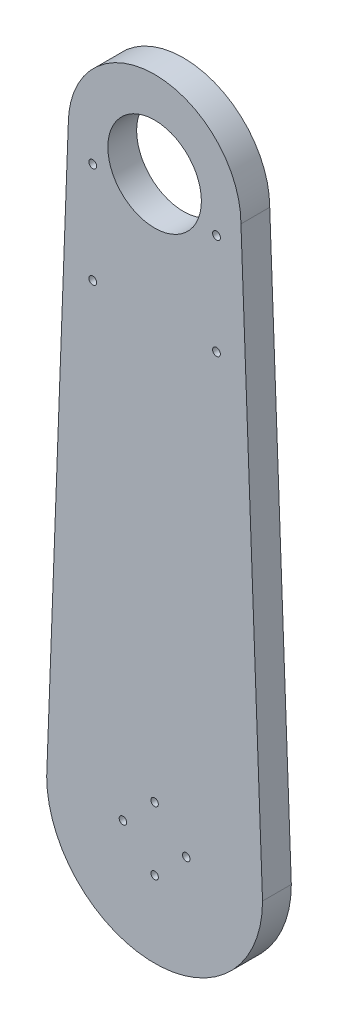
SolidWorks part; units mm, degrees
ref_plane "Front Plane" through (0, 0, 0) normal (0, 0, 1) x (1, 0, 0)
ref_plane "Top Plane" through (0, 0, 0) normal (0, 1, 0) x (1, 0, 0)
ref_plane "Right Plane" through (0, 0, 0) normal (1, 0, 0) x (0, 0, -1)
sketch "Sketch1" plane through (0, 0, 0) normal (0, 0, 1) x (1, 0, 0)
  line L0 (-30, 200) -> (-37.5, 0)
  line L1 (30, 200) -> (37.5, 0)
  circle A0 centre (0, 0) radius 37.5
  circle A1 centre (0, 200) radius 30
  dimension "D1" = 75
  dimension "D2" = 60
  dimension "D3" = 200
extrude "Boss-Extrude1" add sketch "Sketch1" along normal blind 10 contours A1 L0 A0 L1 | A1 | A0 L0
sketch "Sketch3" plane through (0, 0, 0) normal (0, 0, -1) x (-1, 0, 0)
  circle A0 centre (0, 200) radius 16.25
  dimension "D1" = 32.5
extrude "Cut-Extrude4" cut sketch "Sketch3" against normal up to next
sketch "Sketch4" plane through (0, 0, 0) normal (0, 0, -1) x (-1, 0, 0)
  circle A0 centre (0, 0) radius 11 construction
  circle A1 centre (0, 11) radius 1.3
  circle A3 centre (11, 0) radius 1.3
  circle A4 centre (0, -11) radius 1.3
  circle A5 centre (-11, 0) radius 1.3
  point P16 (0, 0)
  dimension "D1" = 2.6
  dimension "D2" = 22
  dimension "D3" = 4
extrude "Cut-Extrude5" cut sketch "Sketch4" against normal up to next
sketch "Sketch5" plane through (0, 0, 0) normal (0, 0, -1) x (-1, 0, 0)
  line L1 (-14.5, 211.25) -> (14.5, 211.25) construction
  line L2 (-14.5, 211.25) -> (-14.5, 164.25) construction
  line L3 (-14.5, 164.25) -> (14.5, 164.25) construction
  line L4 (14.5, 211.25) -> (14.5, 164.25) construction
  line L5 (-14.5, 211.25) -> (14.5, 164.25) construction
  line L6 (-14.5, 164.25) -> (14.5, 211.25) construction
  line L10 (-21.5, 192.25) -> (21.5, 192.25) construction
  line L11 (-21.5, 192.25) -> (-21.5, 157.25) construction
  line L12 (-21.5, 157.25) -> (21.5, 157.25) construction
  line L13 (21.5, 192.25) -> (21.5, 157.25) construction
  line L14 (-21.5, 192.25) -> (21.5, 157.25) construction
  line L15 (-21.5, 157.25) -> (21.5, 192.25) construction
  circle A0 centre (0, 200) radius 10.5 construction
  circle A1 centre (21.5, 157.25) radius 1.35
  circle A2 centre (-21.5, 157.25) radius 1.35
  circle A3 centre (-21.5, 192.25) radius 1.35
  circle A4 centre (21.5, 192.25) radius 1.35
  circle A5 centre (0, 200) radius 10.5 construction
  point P3 (0, 187.75)
  point P12 (0, 174.75)
  dimension "D1" = 21
  dimension "D4" = 2.7
  dimension "D8" = 21
  dimension "D2" = 29
  dimension "D3" = 47
  dimension "D5" = 35
  dimension "D6" = 7
  dimension "D7" = 7
  dimension "D9" = 11.25
extrude "Cut-Extrude6" cut sketch "Sketch5" against normal up to surface (10 mm away) up to face at (1.3, 11, 10)
equation "\"WG_\"= 8"
